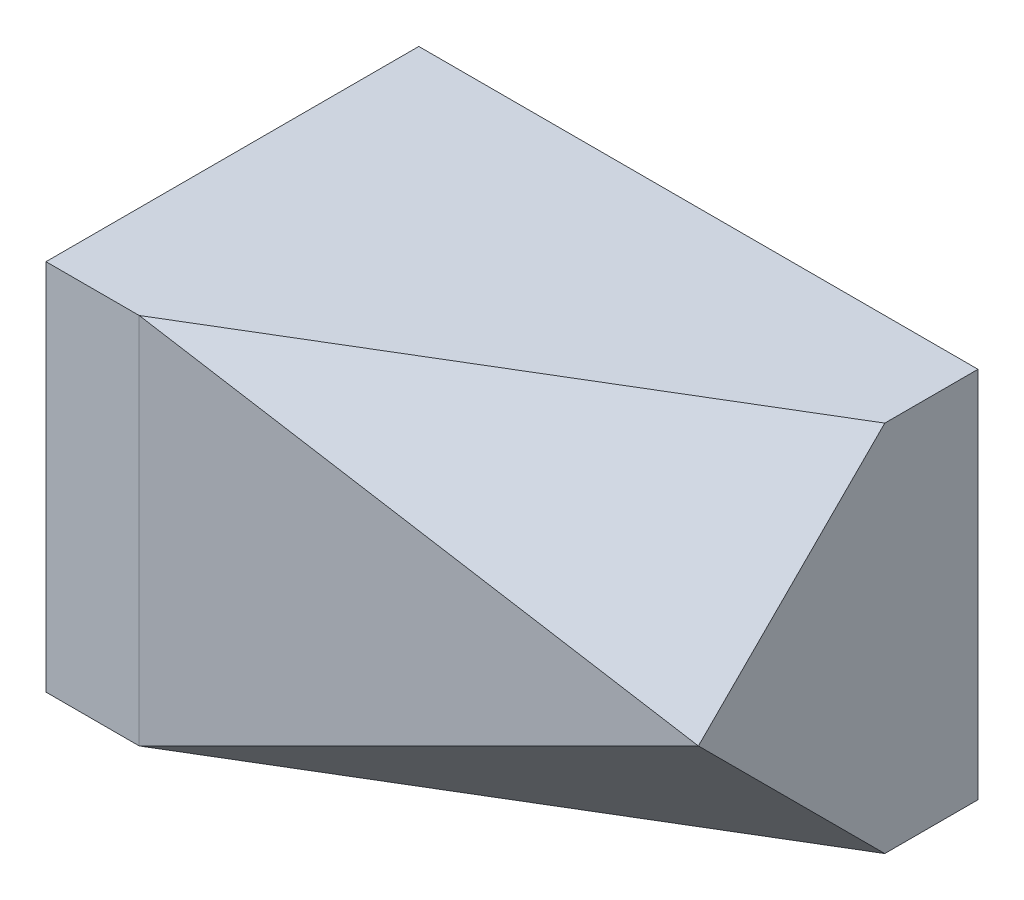
SolidWorks part; units mm, degrees
ref_plane "前基準面" through (0, 0, 0) normal (0, 0, 1) x (1, 0, 0)
ref_plane "上基準面" through (0, 0, 0) normal (0, 1, 0) x (1, 0, 0)
ref_plane "右基準面" through (0, 0, 0) normal (1, 0, 0) x (0, 0, -1)
sketch "草圖1" plane through (0, 0, 0) normal (0, 1, 0) x (1, 0, 0)
  line L0 (15, -5) -> (-10, -10)
  line L1 (15, 10) -> (-15, 10)
  line L2 (15, 10) -> (15, -5)
  line L3 (-10, -10) -> (-15, -10)
  line L4 (-15, 10) -> (-15, -10)
  line L5 (15, 10) -> (-15, -10) construction
  line L6 (9.2308, -6.1538) -> (-15, 10) construction
  point P0 (0, 0)
  dimension "D1" = 20
  dimension "D2" = 30
  dimension "D4" = 5
extrude "填料-伸長1" add sketch "草圖1" along normal blind 20
sketch "草圖2" plane through (0, 20, 0) normal (0, 1, 0) x (1, 0, 0)
  line L0 (-10, -10) -> (15, 5)
  line L1 (15, -5) -> (15, 10) construction
  dimension "D1" = 10
sketch "草圖3" plane through (1.5385, 0, 7.6923) normal (0.1961, 0, 0.9806) x (0.9806, 0, -0.1961)
  line L0 (-11.767, 20) -> (13.7281, 10)
  line L1 (13.7281, 20) -> (13.7281, 0) construction
  dimension "D1" = 10
ref_plane "平面1" through (6.1017, 10.1695, 10.1695) normal (0.3906, 0.6509, 0.6509) x (0.9206, -0.2762, -0.2762)
sketch "草圖4" plane through (6.1017, 10.1695, 10.1695) normal (0.3906, 0.6509, 0.6509) x (0.9206, -0.2762, -0.2762)
  line L1 (-18.2612, 0.9303) -> (21.4199, 0.9303)
  line L2 (-18.2612, 0.9303) -> (-18.2612, 20.5233)
  line L3 (-18.2612, 20.5233) -> (21.4199, 20.5233)
  line L4 (21.4199, 0.9303) -> (21.4199, 20.5233)
extrude "除料-伸長1" cut sketch "草圖4" along normal blind 20
sketch "草圖5" plane through (1.5385, 0, 7.6923) normal (0.1961, 0, 0.9806) x (0.9806, 0, -0.1961)
  line L0 (-11.767, 0) -> (13.7281, 10)
sketch "草圖6" plane through (15, 0, 0) normal (1, 0, 0) x (0, 0, -1)
  line L0 (5, 0) -> (-5, 10)
  line L1 (-5, 0) -> (10, 0) construction
  dimension "D1" = 5
ref_plane "平面2" through (1.0169, -1.6949, 1.6949) normal (-0.3906, 0.6509, -0.6509) x (-0.9206, -0.2762, 0.2762)
sketch "草圖7" plane through (1.0169, -1.6949, 1.6949) normal (-0.3906, 0.6509, -0.6509) x (-0.9206, -0.2762, 0.2762)
  line L1 (-56.3425, -4.1826) -> (75.8506, -4.1826)
  line L2 (-56.3425, -4.1826) -> (-56.3425, 26.0191)
  line L3 (-56.3425, 26.0191) -> (75.8506, 26.0191)
  line L4 (75.8506, -4.1826) -> (75.8506, 26.0191)
extrude "除料-伸長2" cut sketch "草圖7" against normal blind 20
scale "縮放比例1" scale about centroid uniform scaling yes scale factor 0.2
